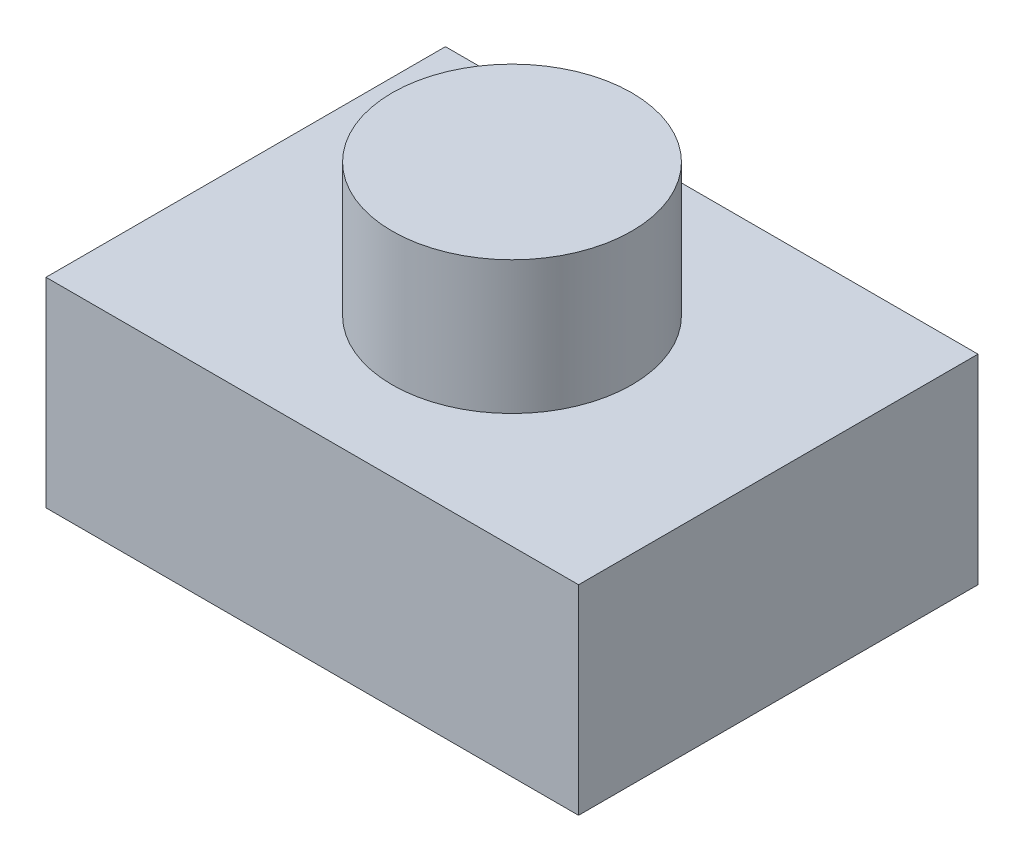
SolidWorks part; units mm, degrees
ref_plane "Front Plane" through (0, 0, 0) normal (0, 0, 1) x (1, 0, 0)
ref_plane "Top Plane" through (0, 0, 0) normal (0, 1, 0) x (1, 0, 0)
ref_plane "Right Plane" through (0, 0, 0) normal (1, 0, 0) x (0, 0, -1)
sketch "Sketch1" plane through (0, 0, 0) normal (0, 1, 0) x (1, 0, 0)
  line L1 (-2, 1.5) -> (2, 1.5)
  line L2 (-2, 1.5) -> (-2, -1.5)
  line L3 (-2, -1.5) -> (2, -1.5)
  line L4 (2, 1.5) -> (2, -1.5)
  point P4 (-2, 0)
  point P6 (2, 0)
  point P8 (0, 1.5)
  point P9 (0, -1.5)
  dimension "D1" = 4
  dimension "D2" = 3
extrude "Boss-Extrude1" add sketch "Sketch1" along normal blind 1.5
sketch "Sketch2" plane through (0, 1.5, 0) normal (0, 1, 0) x (1, 0, 0)
  circle A0 centre (0, 0) radius 0.9
  dimension "D1" = 1.8
extrude "Boss-Extrude2" add sketch "Sketch2" along normal blind 1
